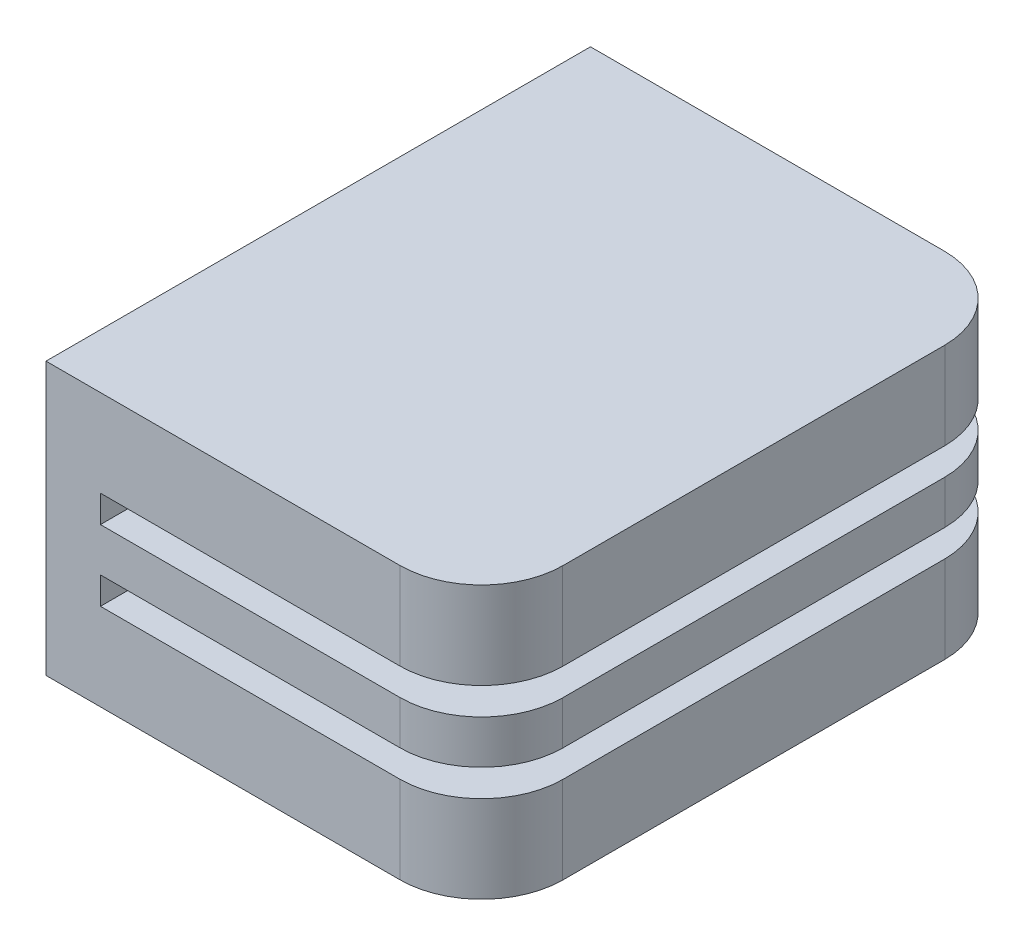
SolidWorks part; units mm, degrees
ref_plane "Front Plane" through (0, 0, 0) normal (0, 0, 1) x (1, 0, 0)
ref_plane "Top Plane" through (0, 0, 0) normal (0, 1, 0) x (1, 0, 0)
ref_plane "Right Plane" through (0, 0, 0) normal (1, 0, 0) x (0, 0, -1)
sketch "Sketch1" plane through (0, 0, 0) normal (0, 1, 0) x (1, 0, 0)
  line L1 (4, -5) -> (-4, -5)
  line L2 (4, -5) -> (4, 5)
  line L3 (4, 5) -> (-4, 5)
  line L4 (-4, -5) -> (-4, 5)
  line L5 (4, -5) -> (-4, 5) construction
  line L6 (4, 5) -> (-4, -5) construction
  point P0 (0, 0)
  dimension "D1" = 10
  dimension "D2" = 8
extrude "Boss-Extrude1" add sketch "Sketch1" against normal blind 5
sketch "Sketch2" plane through (0, 0, -5) normal (0, 0, -1) x (-1, 0, 0)
  line L0 (-4, -1.6) -> (3, -1.6)
  line L1 (-4, -5) -> (-4, 0) construction
  line L2 (3, -1.6) -> (3, -2.1)
  line L3 (3, -2.1) -> (-4, -2.1)
  line L4 (-4, -2.1) -> (-4, -1.6)
  line L5 (-4, -2.5) -> (-4, -2.9) construction
  line L6 (-4, -2.9) -> (-4, -3.4)
  line L7 (-4, -3.4) -> (3, -3.4)
  line L8 (3, -3.4) -> (3, -2.9)
  line L9 (3, -2.9) -> (-4, -2.9)
  line L10 (-4, -2.5) -> (-4, -2.1) construction
  dimension "D1" = 0.8
  dimension "D2" = 7
  dimension "D3" = 0.5
extrude "Cut-Extrude1" cut sketch "Sketch2" against normal up to next
sketch "Sketch3" plane through (0, 0, 0) normal (0, 1, 0) x (1, 0, 0)
  line L0 (2.5, 5) -> (4, 5)
  line L1 (4, 5) -> (4, 3.51)
  line L2 (-4, -5) -> (4, -5) construction
  line L3 (4, -3.51) -> (4, -5)
  line L4 (4, 5) -> (-4, 5) construction
  line L5 (4, -5) -> (4, 5) construction
  line L7 (4, -5) -> (2.5, -5)
  arc A0 (2.5, 5) -> (4, 3.51) centre (2.5, 3.5) cw
  arc A1 (2.5, -5) -> (4, -3.51) centre (2.5, -3.5) ccw
  dimension "D1" = 1.5
extrude "Cut-Extrude3" cut sketch "Sketch3" against normal blind 5
